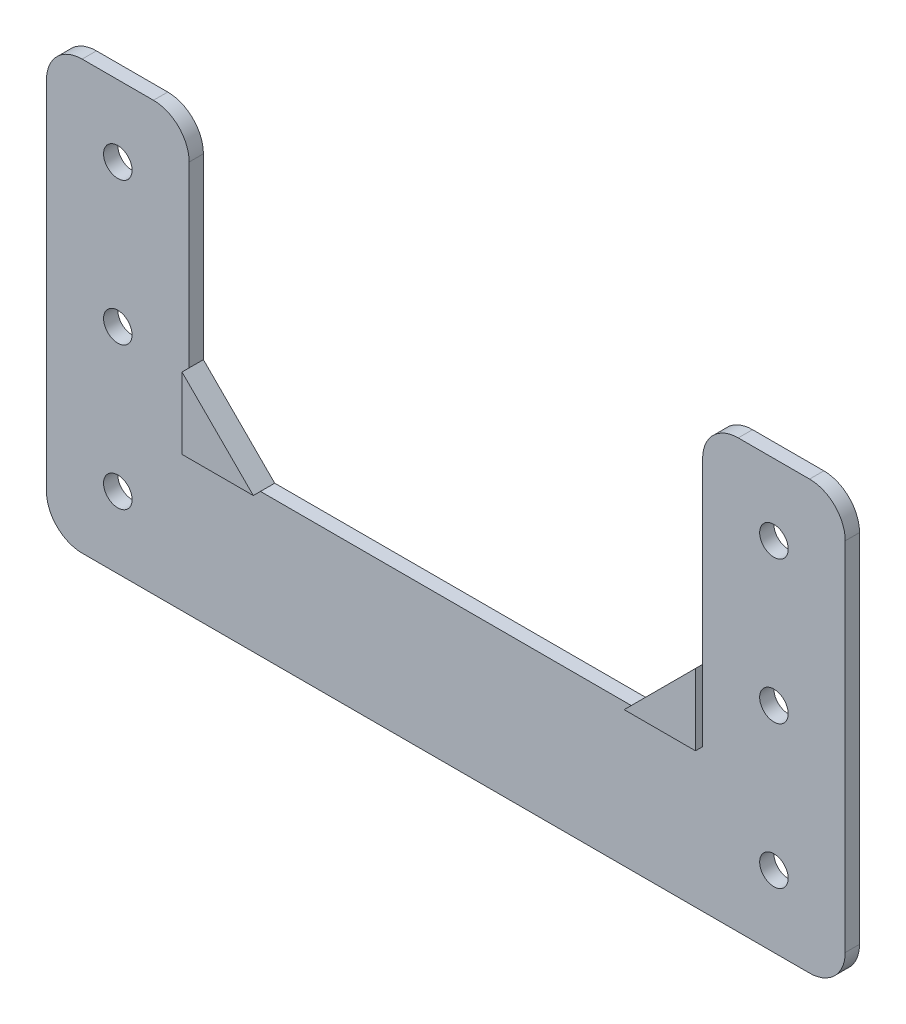
SolidWorks part; units mm, degrees
material "3.1325 (EN-AW 2017A)"
ref_plane "正面" through (0, 0, 0) normal (0, 0, 1) x (1, 0, 0)
ref_plane "平面" through (0, 0, 0) normal (0, 1, 0) x (1, 0, 0)
ref_plane "右側面" through (0, 0, 0) normal (1, 0, 0) x (0, 0, -1)
sketch "ｽｹｯﾁ1" plane through (0, 0, 0) normal (0, 0, 1) x (1, 0, 0)
  line L0 (0, 30) -> (0, -30) construction
  line L1 (-56, -30) -> (56, -30)
  line L2 (-56, -30) -> (-56, 30)
  line L3 (-56, 30) -> (56, 30)
  line L4 (56, -30) -> (56, 30)
  line L5 (-56, -30) -> (56, 30) construction
  line L6 (-56, 30) -> (56, -30) construction
  line L38 (-36, 30) -> (36, 30)
  line L44 (-36, 30) -> (-36, -10)
  line L45 (36, 30) -> (36, -10)
  line L51 (-36, -10) -> (36, -10)
  point P0 (0, 0)
  dimension "D1" = 60
  dimension "D2" = 112
  dimension "D3" = 20
  dimension "D4" = 20
  dimension "D5" = 20
extrude "ﾎﾞｽ - 押し出し1" add sketch "ｽｹｯﾁ1" along normal blind 3
sketch "ｽｹｯﾁ3" plane through (0, 0, 3) normal (0, 0, 1) x (1, 0, 0)
  line L0 (-56, -30) -> (-56, 30) construction
  line L1 (-56, -30) -> (56, -30) construction
  line L2 (56, -30) -> (56, 30) construction
  circle A0 centre (-46, -20) radius 2
  circle A1 centre (46, -20) radius 2
  circle A2 centre (46, 0) radius 2
  circle A3 centre (-46, 0) radius 2
  circle A4 centre (-46, 20) radius 2
  circle A5 centre (46, 20) radius 2
  dimension "D1" = 10
  dimension "D2" = 10
  dimension "D3" = 4
  dimension "D6" = 20
  dimension "D7" = 10
  dimension "D8" = 10
  dimension "D4" = 2
  dimension "D5" = 3
extrude "ｶｯﾄ - 押し出し2" cut sketch "ｽｹｯﾁ3" against normal blind 10
fillet "ﾌｨﾚｯﾄ2" radius 5 6 edges at (-56, -30, 1.5) (56, -30, 1.5) (56, 30, 1.5) (36, 30, 1.5) (-36, 30, 1.5) (-56, 30, 1.5)
chamfer "面取り1" distance 10 angle 45 2 edges at (36, -10, 1.5) (-36, -10, 1.5)
sketch "ｽｹｯﾁ4" plane through (0, 0, 3) normal (0, 0, 1) x (1, 0, 0)
  line L0 (-36, 0) -> (-36, -10)
  line L1 (-36, -10) -> (-26, -10)
  line L2 (26, -10) -> (36, -10)
  line L3 (36, -10) -> (36, 0)
  line L10 (-56, 25) -> (-56, -25)
  line L11 (-51, -30) -> (51, -30)
  line L12 (56, -25) -> (56, 25)
  line L13 (51, 30) -> (41, 30)
  line L14 (36, 25) -> (36, 0)
  line L15 (36, 0) -> (26, -10)
  line L16 (26, -10) -> (-26, -10)
  line L17 (-26, -10) -> (-36, 0)
  line L18 (-36, 0) -> (-36, 25)
  line L19 (-41, 30) -> (-51, 30)
  line L20 (-56, 25) -> (-56, -25)
  line L21 (-51, -30) -> (51, -30)
  line L22 (56, -25) -> (56, 25)
  line L23 (51, 30) -> (41, 30)
  line L24 (36, 25) -> (36, 0)
  line L25 (36, 0) -> (26, -10) construction
  line L26 (26, -10) -> (-26, -10)
  line L27 (-26, -10) -> (-36, 0) construction
  line L28 (-36, 0) -> (-36, 25)
  line L29 (-41, 30) -> (-51, 30)
  arc A6 (-56, -25) -> (-51, -30) centre (-51, -25) ccw
  arc A7 (51, -30) -> (56, -25) centre (51, -25) ccw
  arc A8 (56, 25) -> (51, 30) centre (51, 25) ccw
  arc A9 (41, 30) -> (36, 25) centre (41, 25) ccw
  arc A10 (-36, 25) -> (-41, 30) centre (-41, 25) ccw
  arc A11 (-51, 30) -> (-56, 25) centre (-51, 25) ccw
  arc A12 (-56, -25) -> (-51, -30) centre (-51, -25) ccw
  arc A13 (51, -30) -> (56, -25) centre (51, -25) ccw
  arc A14 (56, 25) -> (51, 30) centre (51, 25) ccw
  arc A15 (41, 30) -> (36, 25) centre (41, 25) ccw
  arc A16 (-36, 25) -> (-41, 30) centre (-41, 25) ccw
  arc A17 (-51, 30) -> (-56, 25) centre (-51, 25) ccw
  dimension "D1" = 0
extrude "ｶｯﾄ - 押し出し3" cut sketch "ｽｹｯﾁ4" against normal blind 1
